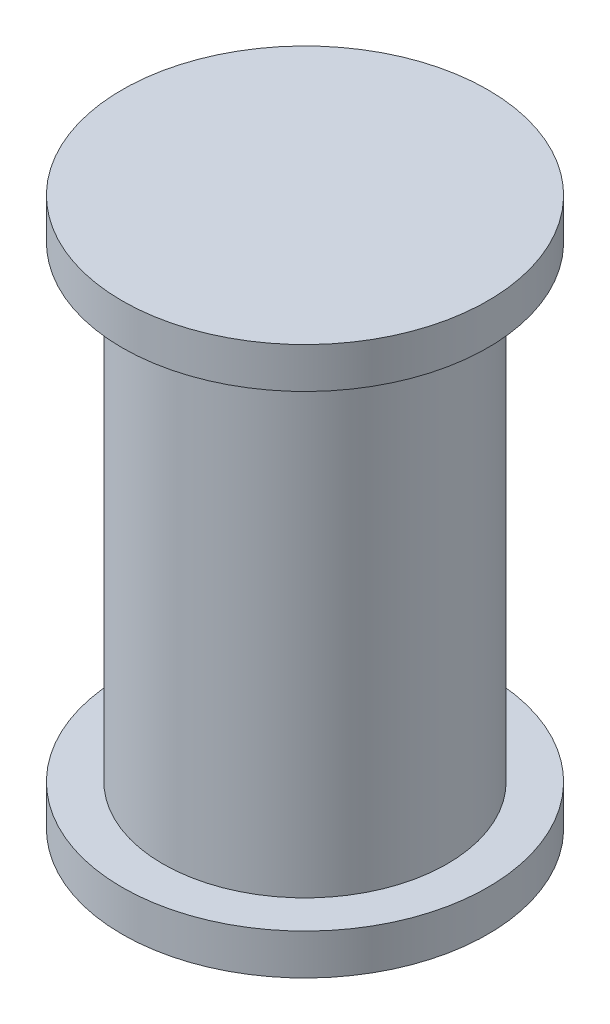
SolidWorks part; units mm, degrees
ref_plane "Front Plane" through (0, 0, 0) normal (0, 0, 1) x (1, 0, 0)
ref_plane "Top Plane" through (0, 0, 0) normal (0, 1, 0) x (1, 0, 0)
ref_plane "Right Plane" through (0, 0, 0) normal (1, 0, 0) x (0, 0, -1)
sketch "Sketch1" plane through (0, 0, 0) normal (1, 0, 0) x (0, 0, -1)
  line L0 (0, 0.4) -> (-1.8, 0.4)
  line L1 (0, 2.09) -> (0, -2.09) construction
  line L2 (-1.8, 0.4) -> (-1.8, 0)
  line L3 (-1.8, 0) -> (-1.4, 0)
  line L6 (0, 0.4) -> (0, -5)
  line L7 (2.09, 0) -> (-2.09, 0) construction
  line L8 (0, -5) -> (-1.8, -5)
  line L9 (-1.8, -5) -> (-1.8, -4.6)
  line L10 (-1.8, -4.6) -> (-1.4, -4.6)
  line L11 (-1.4, 0) -> (-1.4, -4.6)
  dimension "D1" = 1.4
  dimension "D2" = 1.8
  dimension "D3" = 0.4
  dimension "D4" = 5
  dimension "D5" = 0.4
revolve "Revolve1" add sketch "Sketch1" angle 360 about L6
